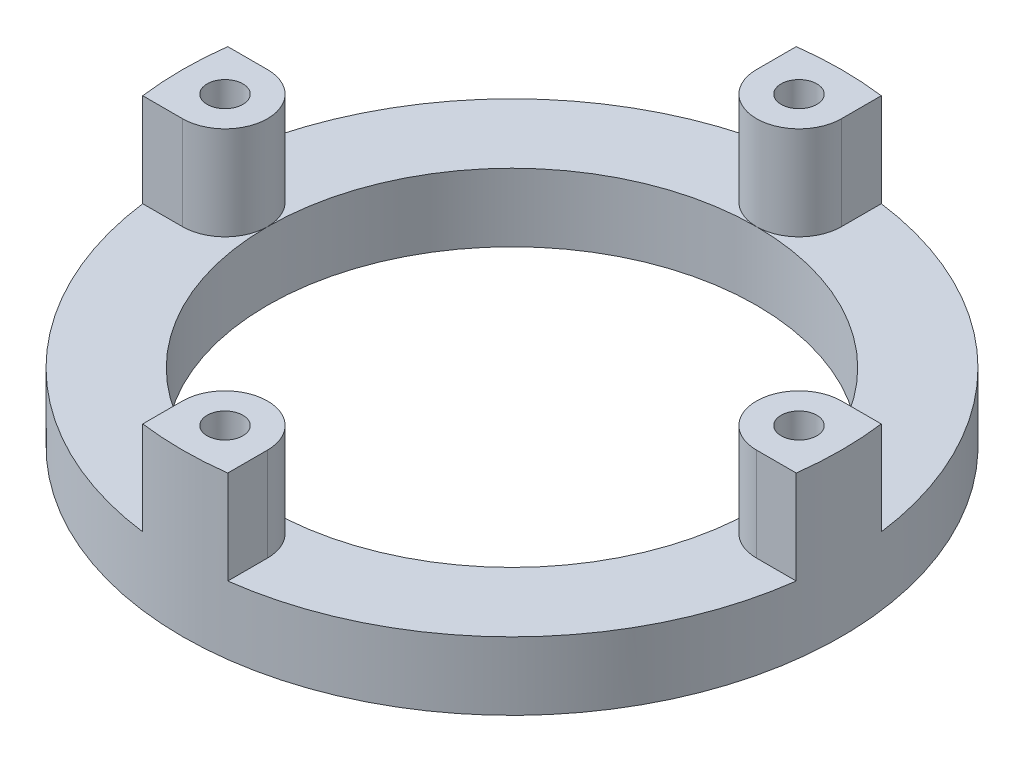
SolidWorks part; units mm, degrees
material "6061-T6 (SS)"
ref_plane "Front Plane" through (0, 0, 0) normal (0, 0, 1) x (1, 0, 0)
ref_plane "Top Plane" through (0, 0, 0) normal (0, 1, 0) x (1, 0, 0)
ref_plane "Right Plane" through (0, 0, 0) normal (1, 0, 0) x (0, 0, -1)
sketch "Sketch1" plane through (0, 0, 0) normal (0, 1, 0) x (1, 0, 0)
  circle A0 centre (0, 0) radius 98.425
  circle A1 centre (0, 0) radius 73.025
  dimension "D1" = 196.85
  dimension "D2" = 146.05
extrude "Boss-Extrude1" add sketch "Sketch1" along normal blind 20.32
sketch "Sketch7" plane through (0, 20.32, 0) normal (0, 1, 0) x (1, 0, 0)
  line L0 (0, -98.425) -> (0, 98.425) construction
  line L1 (-98.425, 0) -> (98.425, 0) construction
  circle A0 centre (0, 0) radius 73.025 construction
sketch "Sketch9" plane through (0, 20.32, 0) normal (0, 1, 0) x (1, 0, 0)
  line L0 (0, 0) -> (0, 98.425) construction
  line L1 (0, 85.725) -> (48.3602, 85.725) construction
  line L2 (0, 85.725) -> (-50.1689, 85.725) construction
  line L6 (-12.7, 85.725) -> (-12.7, 97.6022)
  line L7 (12.7, 85.725) -> (12.7, 97.6022)
  circle A0 centre (0, 85.725) radius 5.334
  arc A4 (12.7, 97.6022) -> (-12.7, 97.6022) centre (0, 0) ccw
  arc A5 (-12.7, 85.725) -> (12.7, 85.725) centre (0, 85.725) ccw
  dimension "D1" = 10.668
  dimension "D3" = 196.85
  dimension "D2" = 85.725
extrude "Boss-Extrude6" add sketch "Sketch9" along normal blind 27.94
pattern_circular "CirPattern5" count 4 over 360 about axis through (0, 0, 0) along (0, 1, 0) of "Boss-Extrude6"
ref_plane "Plane1" through (0, 0, 0) normal (-0.7071, -0.7071, 0) x (-0.7071, 0.7071, 0)
